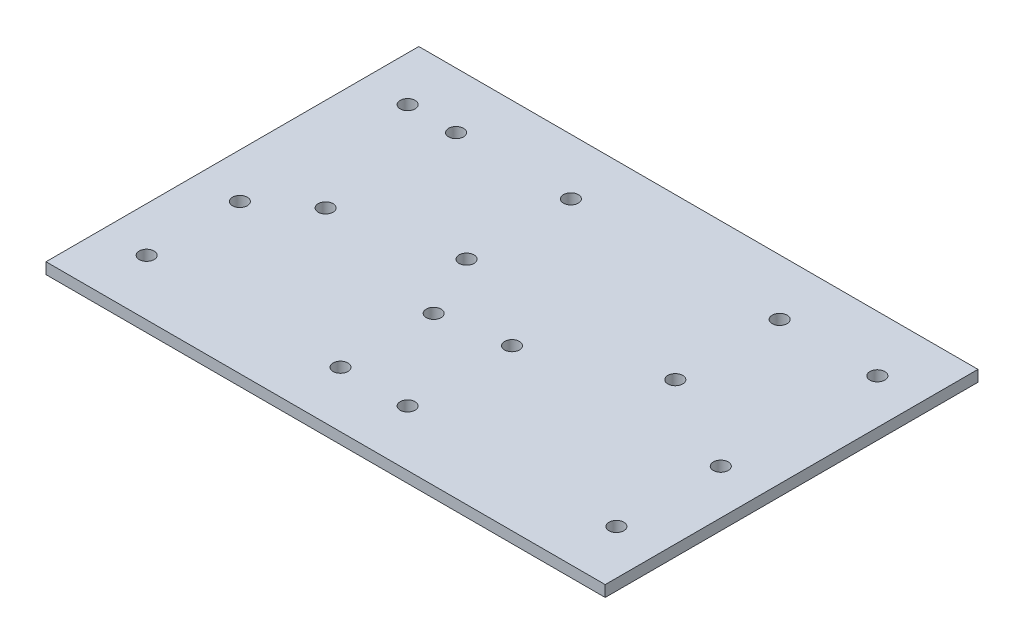
SolidWorks part; units mm, degrees
ref_plane "Front Plane" through (0, 0, 0) normal (0, 0, 1) x (1, 0, 0)
ref_plane "Top Plane" through (0, 0, 0) normal (0, 1, 0) x (1, 0, 0)
ref_plane "Right Plane" through (0, 0, 0) normal (1, 0, 0) x (0, 0, -1)
sketch "Sketch1" plane through (0, 0, 0) normal (0, 1, 0) x (1, 0, 0)
  line L1 (-12, 12.4973) -> (138, 12.4973)
  line L2 (-12, 12.4973) -> (-12, -87.5027)
  line L3 (-12, -87.5027) -> (138, -87.5027)
  line L4 (138, 12.4973) -> (138, -87.5027)
  circle A0 centre (0, -2.5027) radius 2
  circle A1 centre (126, -2.5027) radius 2
  circle A2 centre (0, -72.5027) radius 2
  circle A3 centre (126, -72.5027) radius 2
  dimension "D3" = 4
  dimension "D4" = 4
  dimension "D5" = 126
  dimension "D6" = 12
  dimension "D7" = 4
  dimension "D8" = 4
  dimension "D9" = 126
  dimension "D10" = 70
  dimension "D11" = 12
  dimension "D12" = 15
  dimension "D1" = 150
  dimension "D2" = 100
extrude "Boss-Extrude1" add sketch "Sketch1" along normal blind 3
sketch "Sketch2" plane through (0, 3, 0) normal (0, 1, 0) x (1, 0, 0)
  line L0 (138, 12.4973) -> (-12, 12.4973) construction
  line L1 (-12, -87.5027) -> (138, -87.5027) construction
  line L2 (-12, 12.4973) -> (-12, -87.5027) construction
  circle A0 centre (13, -2.5027) radius 2
  circle A1 centre (13, -37.5027) radius 2
  circle A2 centre (0, -47.5027) radius 2
  circle A3 centre (0, -72.5027) radius 2
  circle A4 centre (52, -47.5027) radius 2
  circle A5 centre (52, -72.5027) radius 2
  circle A6 centre (43.8002, -2.5027) radius 2
  circle A7 centre (43.8002, -30.5027) radius 2
  circle A8 centre (99.8002, -2.5027) radius 2
  circle A9 centre (99.8002, -30.5027) radius 2
  circle A10 centre (70, -44.5027) radius 2
  circle A11 centre (70, -72.5027) radius 2
  circle A12 centre (126, -44.5027) radius 2
  circle A13 centre (0, -72.5027) radius 2 construction
  circle A14 centre (126, -72.5027) radius 2 construction
  dimension "D1" = 4
  dimension "D2" = 4
  dimension "D3" = 25
  dimension "D4" = 15
  dimension "D5" = 4
  dimension "D6" = 4
  dimension "D7" = 25
  dimension "D8" = 15
  dimension "D9" = 0
  dimension "D10" = 52
  dimension "D11" = 25
  dimension "D12" = 35
  dimension "D13" = 12
  dimension "D14" = 28
  dimension "D15" = 15
  dimension "D16" = 56
  dimension "D17" = 28
  dimension "D18" = 56
  dimension "D19" = 52
  dimension "D20" = 0
extrude "Cut-Extrude1" cut sketch "Sketch2" against normal blind 3
